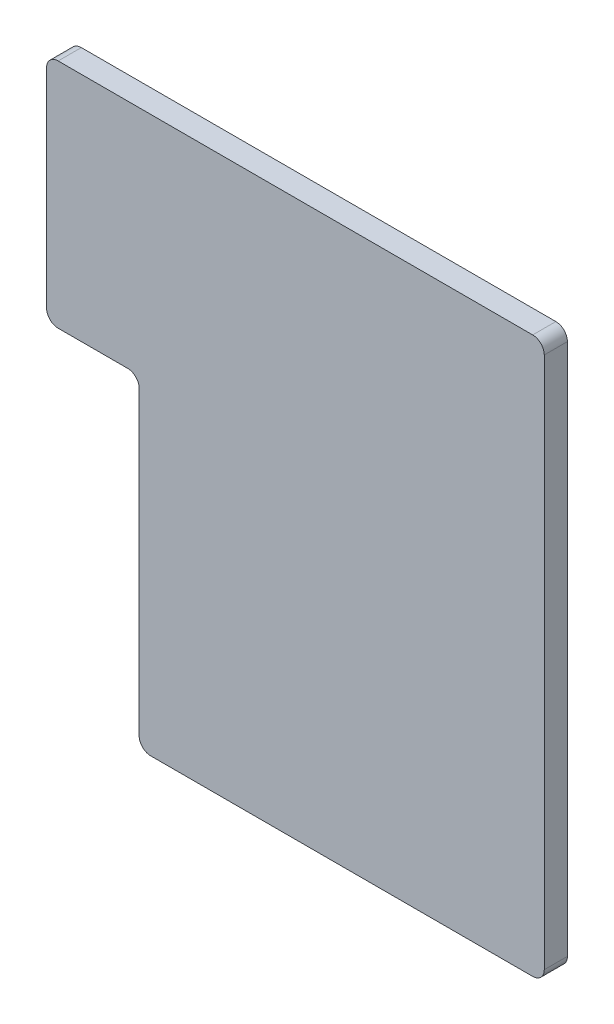
SolidWorks part; units mm, degrees
ref_plane "前视基准面" through (0, 0, 0) normal (0, 0, 1) x (1, 0, 0)
ref_plane "上视基准面" through (0, 0, 0) normal (0, 1, 0) x (1, 0, 0)
ref_plane "右视基准面" through (0, 0, 0) normal (1, 0, 0) x (0, 0, -1)
sketch "草图1" plane through (0, 0, 0) normal (0, 0, 1) x (1, 0, 0)
  line L0 (1.5, 24) -> (-3.5, 24)
  line L1 (0.5, 0) -> (17, 0)
  line L2 (0, 0.5) -> (0, 13.5)
  line L3 (1.5, 24) -> (17, 24)
  line L4 (17.5, 0.5) -> (17.5, 23.5)
  line L5 (-4, 23.5) -> (-4, 14.5)
  line L6 (-3.5, 14) -> (-0.5, 14)
  arc A0 (17, 0) -> (17.5, 0.5) centre (17, 0.5) ccw
  arc A1 (0.5, 0) -> (0, 0.5) centre (0.5, 0.5) cw
  arc A2 (17, 24) -> (17.5, 23.5) centre (17, 23.5) cw
  arc A4 (-0.5, 14) -> (0, 13.5) centre (-0.5, 13.5) cw
  arc A5 (-3.5, 24) -> (-4, 23.5) centre (-3.5, 23.5) ccw
  arc A6 (-4, 14.5) -> (-3.5, 14) centre (-3.5, 14.5) ccw
  point P9 (0, 0)
  point P12 (17.5, 24)
  point P15 (0, 24)
  point P19 (0, 14)
  point P22 (-4, 24)
  point P25 (-4, 14)
  dimension "D3" = 0.5
  dimension "D6" = 0.5
  dimension "D5" = 0.5
  dimension "D1" = 24
  dimension "D2" = 17.5
  dimension "D4" = 10
  dimension "4" = 4
extrude "凸台-拉伸1" add sketch "草图1" along normal blind 1
